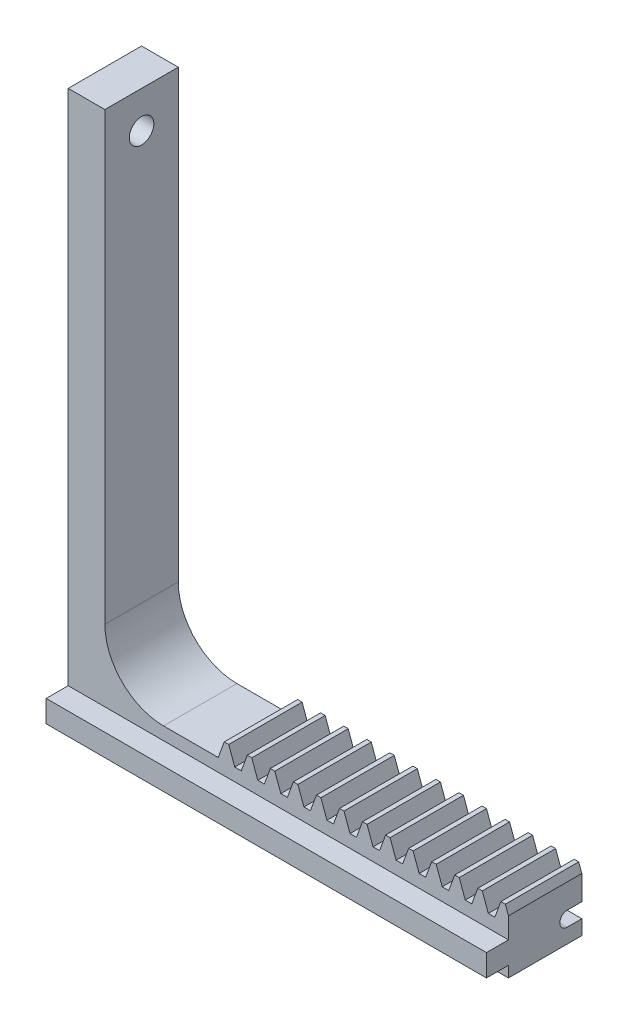
SolidWorks part; units mm, degrees
material "PLA"
ref_plane "Front Plane" through (0, 0, 0) normal (0, 0, 1) x (1, 0, 0)
ref_plane "Top Plane" through (0, 0, 0) normal (0, 1, 0) x (1, 0, 0)
ref_plane "Right Plane" through (0, 0, 0) normal (1, 0, 0) x (0, 0, -1)
sketch "HoldingSke" plane through (0, 0, 0) normal (0, 1, 0) x (1, 0, 0)
  line L0 (0, 0) -> (0.1392, 0.9903)
  line L1 (-15, 0) -> (100, 0) construction
  line L2 (0, 0) -> (-2.1039, 2.3779)
  line L3 (0, 0) -> (-11.863, 4.5341)
  line L4 (0, 0) -> (8.3795, 2.0892)
  line L5 (0, 0) -> (-23.7986, -8.8762)
  line L6 (0, 0) -> (-10.5278, -7.1032)
  line L9 (-71.009, 38.7566) -> (-33.4213, 52.4374)
  line L10 (-76.2, 3.3779) -> (-68.7, 3.3779)
  line L11 (0, 0) -> (-10, 0)
  line L12 (-76.2, 101.6) -> (-76.162, 101.6)
  line L13 (24.9733, 27.94) -> (52.9518, 28.4284)
  line L14 (24.9733, 27.94) -> (24.9743, 27.94)
  line L15 (24.9733, 27.94) -> (100.4006, 29.5858)
  circle A0 centre (0, 0) radius 19.05
  circle A1 centre (0, 0) radius 3.75
  circle A2 centre (0, 0) radius 12.7
  dimension "MPH" = 7.5
  dimension "Diameter" = 38.1
  dimension "Num_teeth" = 14
  dimension "Pitch" = 1
  dimension "Width" = 10
  dimension "Show_teeth" = 998
  dimension "Thickness" = 12.7
  dimension "Ap" = 20
  dimension "Pitch_height" = 7.5
  dimension "Backlash" = 0.038
  dimension "Addendum_fac" = 1
  dimension "Dedendum_fac" = 1.25
  dimension "Clearance_fac" = 0.25
  dimension "Dedendum_add" = 0.001
  dimension "Length" = 40
  dimension "Module" = 1
sketch "BlankSke" plane through (0, 0, 0) normal (0, 0, 1) x (1, 0, 0)
  line L1 (0, 0) -> (40, 0)
  line L2 (0, 0) -> (0, 8.5)
  line L3 (0, 8.5) -> (40, 8.5)
  line L4 (40, 0) -> (40, 8.5)
  dimension "Length" = 40
  dimension "Blank_height" = 8.5
extrude "Blank" add sketch "BlankSke" against normal blind 10
sketch "TooCutSkeIll" plane through (0, 0, 0) normal (0, 0, 1) x (1, 0, 0)
  line L0 (-1.2538, 8.4737) -> (-0.5045, 6.4152)
  line L1 (-0.2687, 6.25) -> (0.2687, 6.25)
  line L2 (0.5045, 6.4152) -> (1.2538, 8.4737)
  line L3 (40, 8.5) -> (0, 8.5) construction
  line L4 (0, 0) -> (0, 64.897) construction
  line L5 (-13.208, 7.5) -> (12.954, 7.5) construction
  line L6 (0, 0) -> (40, 0) construction
  line L7 (0.8994, 7.5) -> (0.8994, 48.7463) construction
  line L8 (-0.8994, 7.5) -> (-0.8994, 48.7463) construction
  line L9 (1.2914, 8.5) -> (1.2914, 8.5254)
  line L10 (-1.2914, 8.5) -> (-1.2914, 8.5254)
  line L11 (-1.2914, 8.5254) -> (1.2914, 8.5254)
  arc A0 (0.2687, 6.25) -> (0.5045, 6.4152) centre (0.2687, 6.501) ccw
  arc A1 (-0.5045, 6.4152) -> (-0.2687, 6.25) centre (-0.2687, 6.501) ccw
  arc A2 (1.2914, 8.5) -> (1.2538, 8.4737) centre (1.2914, 8.46) ccw
  arc A3 (-1.2538, 8.4737) -> (-1.2914, 8.5) centre (-1.2914, 8.46) ccw
  dimension "Root_fillet" = 0.251
  dimension "Break_rad" = 0.04
  dimension "Pitch_height" = 7.5
  dimension "Gap_width" = 1.7988
  dimension "Dedendum" = 1.25
  dimension "Addendum_plus" = 1.0254
  dimension "Pressure_angle" = 20
extrude "ToothCutIll" [suppressed] cut sketch "TooCutSkeIll" against normal through all
sketch "TooCutSkeSim" plane through (0, 0, 0) normal (0, 0, 1) x (1, 0, 0)
  line L0 (0.4444, 6.25) -> (-0.4444, 6.25)
  line L1 (1.2726, 8.5254) -> (0.4444, 6.25)
  line L2 (0, 17.4625) -> (0, 53.467) construction
  line L3 (1.2726, 8.5254) -> (-1.2726, 8.5254)
  line L6 (-1.2726, 8.5254) -> (-0.4444, 6.25)
  line L9 (-0.8994, 7.5) -> (0.8994, 7.5) construction
  line L10 (0, 0) -> (40, 0) construction
  line L11 (0.8994, 7.5) -> (0.8994, 53.467) construction
  line L12 (-0.8994, 7.5) -> (-0.8994, 53.467) construction
  dimension "Pitch_height" = 7.5
  dimension "Pressure_angle" = 20
  dimension "Gap_width" = 1.7988
  dimension "Dedendum" = 1.25
  dimension "Addendum_plus" = 1.0254
extrude "ToothCutSim" cut sketch "TooCutSkeSim" against normal through all
pattern_linear "TeethCuts" count 13 spacing 3.1416 along (1, 0, 0) of "ToothCutIll", "ToothCutSim"
sketch "Sketch1" plane through (0, 0, 0) normal (0, 0, 1) x (1, 0, 0)
  line L5 (0, 0) -> (-20, 0)
  line L10 (-20, 0) -> (-20, 75)
  line L11 (-20, 75) -> (-10, 75)
  line L12 (-10, 75) -> (-10, 6.25)
  line L13 (-10, 6.25) -> (0, 6.25)
  line L14 (0, 6.25) -> (0, 0)
  dimension "D1" = 10
  dimension "D2" = 10
  dimension "D3" = 75
extrude "Boss-Extrude1" add sketch "Sketch1" against normal up to surface (10 mm away) up to face at (20.0266, 7.1062, -10)
other "Move Face1" [suppressed] parameters "D1"=2
sketch "Sketch2" plane through (40, 0, 0) normal (1, 0, 0) x (0, 0, -1)
  line L0 (0, 0) -> (0, 7.3387) construction
  line L1 (0, 4.5) -> (-3, 4.5)
  line L2 (0, 4.5) -> (0, 1.5)
  line L3 (0, 1.5) -> (-3, 1.5)
  line L4 (-3, 4.5) -> (-3, 1.5)
  line L5 (10, 0) -> (10, 7.3387) construction
  line L6 (10, 4.5) -> (13, 4.5) construction
  line L7 (10, 4.5) -> (10, 1.5) construction
  line L8 (10, 1.5) -> (13, 1.5) construction
  line L9 (13, 4.5) -> (13, 1.5) construction
  line L10 (10, 0) -> (0, 0) construction
  point P12 (-3, 3)
  point P13 (13, 3)
  point P16 (10, 3)
  line M10 (0, 7.3387) -> (0, 0)
  dimension "D1" = 3
  dimension "D2" = 3
  dimension "D3" = 3
extrude "Boss-Extrude2" add sketch "Sketch2" against normal up to surface (60 mm away) contours L1 L4 L3 M10 | L7 L6 L9 L8 up to face at (-20, 37.5, -5)
sketch "Sketch5" plane through (40, 0, 0) normal (1, 0, 0) x (0, 0, -1)
  line L0 (10, 0) -> (10, 7.3387) construction
  line L1 (10, 4) -> (8, 4)
  line L2 (10, 4) -> (10, 2)
  line L3 (10, 2) -> (8, 2)
  line L4 (8, 4) -> (8, 2) construction
  line L5 (-3, 4.5) -> (-3, 1.5) construction
  arc A0 (8, 4) -> (8, 2) centre (8, 3) ccw
  point P8 (-3, 3)
  point P9 (8, 3)
  dimension "D1" = 2
  dimension "D2" = 2
extrude "Cut-Extrude2" cut sketch "Sketch5" against normal through all
other "Move Face2" face at (-10, 40.625, -5) parameters "D1"=5
fillet "Fillet2" radius 8 1 edges at (-15, 6.25, -5)
sketch "Sketch3" plane through (-15, 0, 0) normal (-1, 0, 0) x (0, 0, 1)
  line L3 (-10, 75) -> (0, 75) construction
  line L4 (-10, 75) -> (0, 75) construction
  circle A0 centre (-5, 70) radius 1.675
  point P5 (-5, 75)
  dimension "D1" = 3.35
  dimension "D2" = 5
extrude "Cut-Extrude1" cut sketch "Sketch3" along normal through all
ref_plane "Midplane" through (0, 0, -5) normal (0, 0, 1) x (1, 0, 0)
sketch "Sketch4" plane through (0, 0, -5) normal (0, 0, 1) x (1, 0, 0)
  line L0 (46.6697, 7.5) -> (101.4539, 7.5) construction
  line L1 (1.8782, 8.5) -> (1.2634, 8.5) construction
  dimension "D1" = 1
fillet "Fillet3" [suppressed] radius 1
fillet "Fillet4" [suppressed] radius 1
